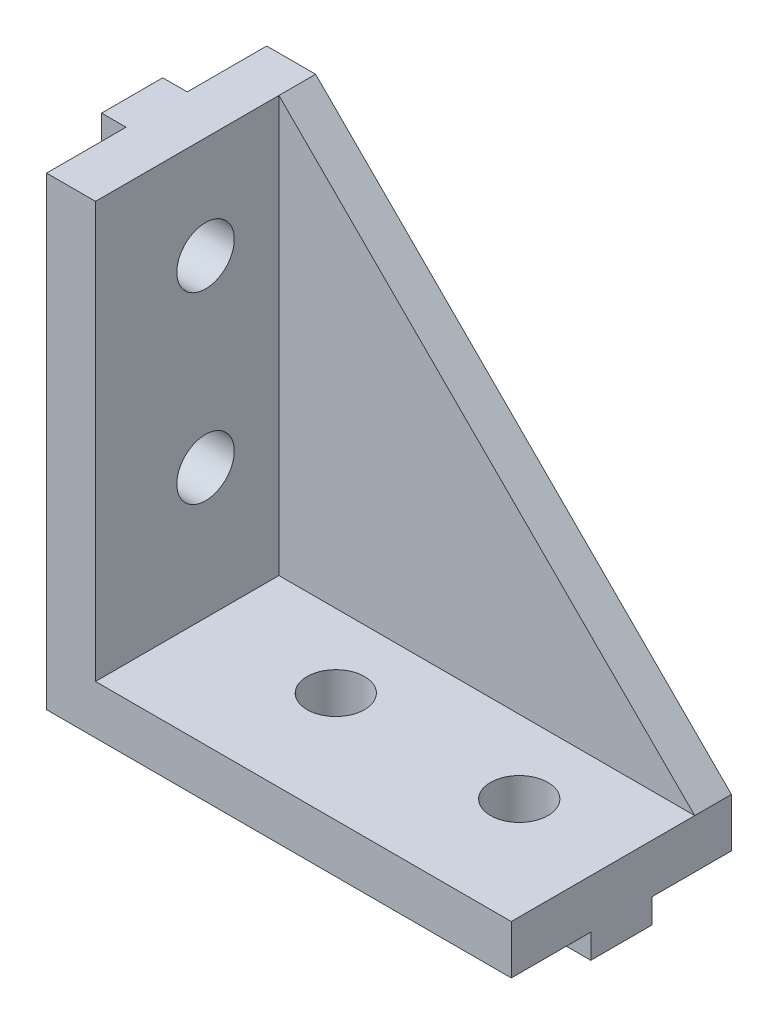
SolidWorks part; units mm, degrees
material "Алюминиевый сплав"
ref_plane "Спереди" through (0, 0, 0) normal (0, 0, 1) x (1, 0, 0)
ref_plane "Сверху" through (0, 0, 0) normal (0, 1, 0) x (1, 0, 0)
ref_plane "Справа" through (0, 0, 0) normal (1, 0, 0) x (0, 0, -1)
sketch "Эскиз1" plane through (0, 0, 0) normal (0, 0, 1) x (1, 0, 0)
  line L0 (0, 38) -> (0, 0)
  line L1 (0, 0) -> (38, 0)
  line L2 (38, 0) -> (38, 4)
  line L4 (4, 38) -> (0, 38)
  line L5 (4, 38) -> (4, 4)
  line L6 (4, 4) -> (38, 4)
  dimension "D1" = 38
  dimension "D2" = 4
extrude "Бобышка-Вытянуть1" add sketch "Эскиз1" along normal mid plane 18
sketch "Эскиз2" plane through (0, 0, -9) normal (0, 0, 1) x (1, 0, 0)
  line L0 (4, 38) -> (38, 4)
  line L1 (38, 4) -> (4, 4)
  line L2 (4, 4) -> (4, 38)
sketch "Эскиз3" plane through (0, 4, 0) normal (0, 1, 0) x (1, 0, 0)
  line L0 (0, 0) -> (14.65, 0) construction
  line L4 (14.65, 0) -> (29.65, 0) construction
  line L5 (38, -9) -> (38, 9) construction
  circle A2 centre (14.65, 0) radius 2.35
  circle A3 centre (29.65, 0) radius 2.35
  dimension "D2" = 8.35
  dimension "D3" = 4.7
  dimension "D1" = 15
extrude "Вырез-Вытянуть1" cut sketch "Эскиз3" against normal through all
sketch "Эскиз4" plane through (0, 0, 0) normal (0, -1, 0) x (1, 0, 0)
  line L1 (0, -2.5) -> (2, -2.5)
  line L2 (0, -2.5) -> (0, 2.5)
  line L3 (0, 2.5) -> (2, 2.5)
  line L4 (2, -2.5) -> (2, 2.5)
  line L5 (0, -2.5) -> (2, 2.5) construction
  line L6 (0, 2.5) -> (2, -2.5) construction
  line L7 (36, -2.5) -> (38, -2.5)
  line L8 (36, -2.5) -> (36, 2.5)
  line L9 (36, 2.5) -> (38, 2.5)
  line L10 (38, -2.5) -> (38, 2.5)
  line L11 (36, -2.5) -> (38, 2.5) construction
  line L12 (36, 2.5) -> (38, -2.5) construction
  line L14 (38, 9) -> (38, -9) construction
  line L15 (0, 9) -> (0, -9) construction
  point P0 (1, 0)
  point P5 (37, 0)
  dimension "D2" = 2
  dimension "D3" = 5
extrude "Бобышка-Вытянуть3" add sketch "Эскиз4" along normal blind 2
ref_plane "Плоскость1" through (0, 0, 0) normal (-0.7071, 0.7071, 0) x (0.7071, 0.7071, 0)
mirror "Зеркальное отражение3" about plane through (0, 0, 0) normal (-0.7071, 0.7071, 0) of "Бобышка-Вытянуть3", "Вырез-Вытянуть1"
extrude "Бобышка-Вытянуть4" add sketch "Эскиз2" along normal blind 3
